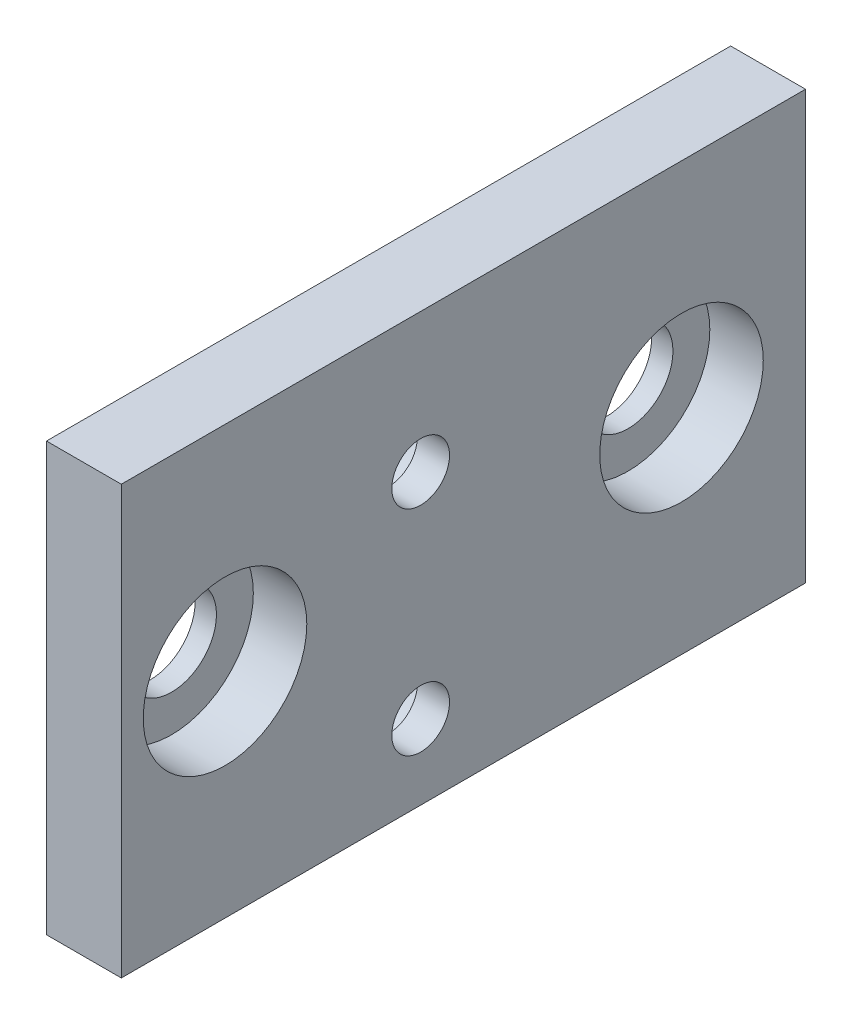
SolidWorks part; units mm, degrees
ref_plane "Alzado" through (0, 0, 0) normal (0, 0, 1) x (1, 0, 0)
ref_plane "Planta" through (0, 0, 0) normal (0, 1, 0) x (1, 0, 0)
ref_plane "Vista lateral" through (0, 0, 0) normal (1, 0, 0) x (0, 0, -1)
sketch "Croquis1" plane through (0, 0, 0) normal (1, 0, 0) x (0, 0, -1)
  line L1 (-10.5, -10) -> (10.5, -10)
  line L2 (-10.5, -10) -> (-10.5, 10)
  line L3 (-10.5, 10) -> (10.5, 10)
  line L4 (10.5, -10) -> (10.5, 10)
  line L5 (-10.5, -10) -> (10.5, 10) construction
  line L6 (-10.5, 10) -> (10.5, -10) construction
  point P0 (0, 0)
  dimension "D1" = 20
  dimension "D2" = 21
extrude "Saliente-Extruir1" add sketch "Croquis1" along normal blind 5
sketch "Croquis2" plane through (5, 0, 0) normal (1, 0, 0) x (0, 0, -1)
  line L0 (-7.5, 3.5) -> (-7.5, -6.5) construction
  line L1 (-7.5, -1.5) -> (-10.5, -1.5) construction
  line L3 (-7.5, 3.5) -> (-10.5, -1.5) construction
  line L4 (-10.5, -1.5) -> (-7.5, -6.5) construction
  line L5 (-10.5, 10) -> (-10.5, -10) construction
  line L6 (-10.5, -10) -> (10.5, -10) construction
  circle A0 centre (-7.5, 3.5) radius 1.35
  circle A1 centre (-7.5, -6.5) radius 1.35
  dimension "D1" = 2.7
  dimension "D2" = 10
  dimension "D3" = 3
  dimension "D4" = 8.5
extrude "Cortar-Extruir1" cut sketch "Croquis2" against normal through all
sketch "Croquis3" plane through (0, 0, 0) normal (-1, 0, 0) x (0, 0, 1)
  circle A0 centre (7.5, 3.5) radius 2.5
  circle A1 centre (7.5, -6.5) radius 2.5
  dimension "D1" = 5
extrude "Cortar-Extruir2" cut sketch "Croquis3" against normal blind 2
sketch "Croquis4" plane through (5, 0, 0) normal (1, 0, 0) x (0, 0, -1)
  line L0 (4.7, 0) -> (10.5, 0) construction
  line L1 (10.5, -10) -> (10.5, 10) construction
  circle A0 centre (4.7, 0) radius 2.1
  circle A1 centre (4.7, 0) radius 3.5 construction
  dimension "D1" = 4.2
  dimension "D2" = 7
  dimension "D3" = 5.8
extrude "Cortar-Extruir3" cut sketch "Croquis4" against normal through all
sketch "Croquis5" plane through (5, 0, 0) normal (1, 0, 0) x (0, 0, -1)
  circle A0 centre (4.7, 0) radius 3.825
  dimension "D1" = 7.65
extrude "Cortar-Extruir4" cut sketch "Croquis5" against normal blind 4
sketch "Croquis7" plane through (5, 0, 0) normal (1, 0, 0) x (0, 0, -1)
  line L1 (-10.5, 10) -> (10.5, 10)
  line L2 (-10.5, 10) -> (-10.5, -10)
  line L3 (-10.5, -10) -> (10.5, -10)
  line L4 (10.5, 10) -> (10.5, -10)
extrude "Cortar-Extruir5" cut sketch "Croquis7" against normal blind 2
sketch "Croquis8" plane through (0, 0, 10.5) normal (0, 0, 1) x (1, 0, 0)
  line L4 (3, -10) -> (3, 10)
  line L5 (3, 10) -> (0, 10)
  line L6 (0, 10) -> (0, -10)
  line L7 (0, -10) -> (3, -10)
  line L8 (3, -10) -> (3, 10)
  line L9 (3, 10) -> (0, 10)
  line L10 (0, 10) -> (0, -10)
  line L11 (0, -10) -> (3, -10)
  dimension "D1" = 0
extrude "Saliente-Extruir2" add sketch "Croquis8" along normal blind 11
sketch "Croquis9" plane through (3, 0, 0) normal (1, 0, 0) x (0, 0, -1)
  line L0 (-16.65, 0) -> (4.7, 0) construction
  circle A0 centre (-16.65, 0) radius 2.1
  circle A2 centre (4.7, 0) radius 2.1 construction
  circle A3 centre (-16.65, 0) radius 3.825 construction
  circle A4 centre (4.7, 0) radius 3.825 construction
  dimension "D1" = 21.35
extrude "Cortar-Extruir6" cut sketch "Croquis9" against normal through all
sketch "Croquis10" plane through (3, 0, 0) normal (1, 0, 0) x (0, 0, -1)
  circle A0 centre (-16.65, 0) radius 3.825
  circle A1 centre (4.7, 0) radius 3.825 construction
extrude "Cortar-Extruir7" cut sketch "Croquis10" against normal blind 2
sketch "Croquis11" plane through (3, 0, 0) normal (1, 0, 0) x (0, 0, -1)
  line L4 (10.5, 10) -> (-21.5, 10)
  line L5 (-21.5, 10) -> (-21.5, -10)
  line L6 (-21.5, -10) -> (10.5, -10)
  line L7 (10.5, -10) -> (10.5, 10)
  line L8 (10.5, 10) -> (-21.5, 10)
  line L9 (-21.5, 10) -> (-21.5, -10)
  line L10 (-21.5, -10) -> (10.5, -10)
  line L11 (10.5, -10) -> (10.5, 10)
  circle A0 centre (-16.65, 0) radius 3.825 construction
  circle A2 centre (-7.5, 3.5) radius 1.35 construction
  circle A3 centre (-7.5, -6.5) radius 1.35 construction
  circle A5 centre (4.7, 0) radius 3.825 construction
  circle A6 centre (-16.65, 0) radius 3.825
  circle A8 centre (-7.5, 3.5) radius 1.35
  circle A9 centre (-7.5, -6.5) radius 1.35
  circle A11 centre (4.7, 0) radius 3.825
  dimension "D1" = 0
extrude "Saliente-Extruir3" add sketch "Croquis11" along normal blind 0.5
move or copy body "Sólido-Mover/Copiar1" [suppressed] bodies to move or copy 110
